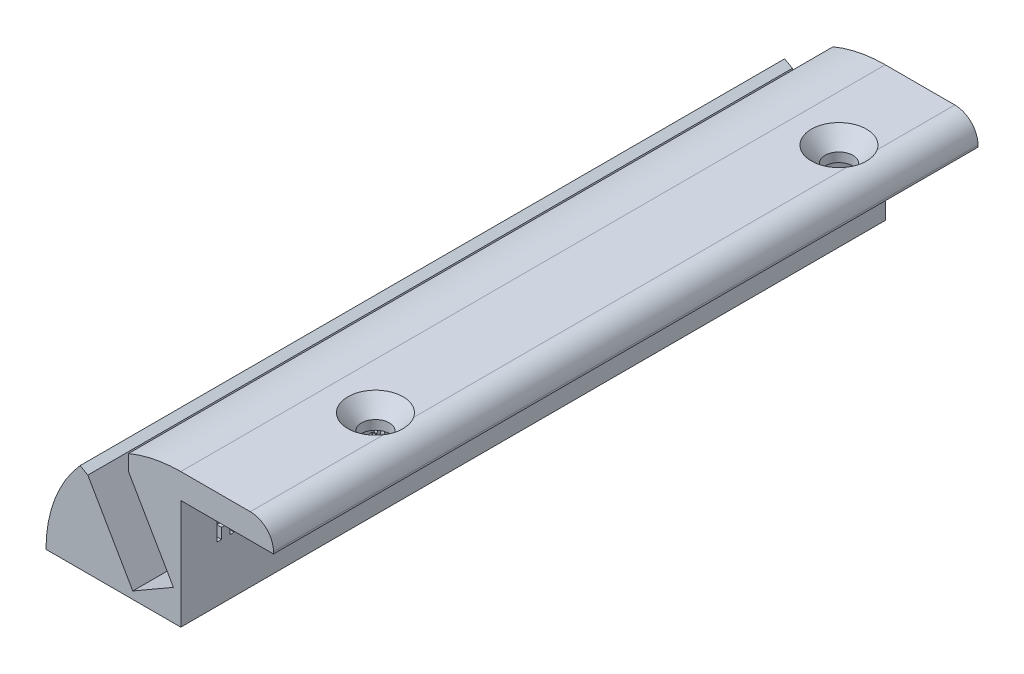
SolidWorks part; units mm, degrees
ref_plane "Front Plane" through (0, 0, 0) normal (0, 0, 1) x (1, 0, 0)
ref_plane "Top Plane" through (0, 0, 0) normal (0, 1, 0) x (1, 0, 0)
ref_plane "Right Plane" through (0, 0, 0) normal (1, 0, 0) x (0, 0, -1)
sketch "Sketch1" plane through (0, 0, 0) normal (0, 0, 1) x (1, 0, 0)
  line L0 (-43.8658, 7.3279) -> (-25.4, 7.3279)
  line L1 (-127, 7.3279) -> (127, 7.3279) construction
  line L2 (-25.4, 7.3279) -> (-25.4, 21.9837)
  line L3 (-25.4, 22.3647) -> (-14.6818, 22.3647)
  line L4 (-25.4, 21.9837) -> (228.6, 21.9837) construction
  line L5 (-25.4, 22.3647) -> (-25.4, 21.9837)
  line L6 (-38.1345, 19.0062) -> (-41.9445, 21.2059)
  line L7 (-41.9445, 21.2059) -> (-32.5693, 26.6187)
  line L8 (-32.5693, 26.6187) -> (-32.5693, 22.2193)
  line L9 (-25.4, 7.3279) -> (-34.6329, 23.3198) construction
  line L14 (-25.4, 25.7937) -> (-15.875, 25.7937)
  line L15 (-12.7, 22.6187) -> (-12.7, 22.3647)
  line L16 (-12.7, 22.3647) -> (-14.6818, 22.3647)
  line L18 (-38.1345, 19.0062) -> (-31.975, 8.3377)
  line L19 (-31.975, 8.3377) -> (-26.4098, 11.5508)
  line L20 (-26.4098, 11.5508) -> (-32.5693, 22.2193)
  line L21 (-32.5693, 22.2193) -> (-38.1345, 19.0062)
  line L22 (-38.1345, 19.0062) -> (-31.975, 8.3377)
  line L23 (-31.975, 8.3377) -> (-26.4098, 11.5508)
  line L24 (-26.4098, 11.5508) -> (-32.5693, 22.2193)
  line L25 (-32.5693, 22.2193) -> (-38.1345, 19.0062)
  circle A0 centre (-25.4, 7.3279) radius 18.4658
  arc A1 (-15.875, 25.7937) -> (-12.7, 22.6187) centre (-15.875, 22.6187) cw
  point P3 (-25.4, 25.7937)
  point P7 (-25.4, 21.9837)
  point P20 (-27.0497, 10.1852)
  dimension "D8" = 3.175
  dimension "D1" = 3.81
  dimension "D2" = 0.381
  dimension "D3" = 60
  dimension "D4" = 0.1905
  dimension "D5" = 30
  dimension "D6" = 30
  dimension "D7" = 3.81
  dimension "D9" = 12.7
extrude "Boss-Extrude1" add sketch "Sketch1" along normal mid plane 96.52 contours L0 L9 L23 L22 L6 A0 | L9 L2 L5 L3 A0 L8 L24 L23 | A1 L14 A0 L16 L15
ref_plane "Plane1" through (0, 0, -35.56) normal (0, 0, -1) x (-1, 0, 0)
sketch "Sketch4" plane through (0, 0, -35.56) normal (0, 0, -1) x (-1, 0, 0)
  line L0 (20.955, 22.3647) -> (20.955, 23.6347)
  line L1 (25.4, 22.3647) -> (12.7, 22.3647) construction
  line L2 (20.955, 23.6347) -> (24.267, 27.4447)
  line L3 (24.267, 27.4447) -> (19.05, 27.4447)
  line L4 (19.05, 27.4447) -> (19.05, 22.3647)
  line L5 (19.05, 22.3647) -> (20.955, 22.3647)
  point P7 (21.1325, 23.6347)
  dimension "D1" = 1.905
  dimension "D2" = 1.27
  dimension "D3" = 41
  dimension "D4" = 5.08
  dimension "D5" = 6.35
revolve "Cut-Revolve1" cut sketch "Sketch4" angle 360 about L4
pattern_linear "LPattern1" count 2 spacing 63.5 along (0, 0, 1) of "Cut-Revolve1"
sketch "Sketch5" plane through (-25.4, 0, 0) normal (1, 0, 0) x (0, 0, -1)
  line L0 (-69.1647, 14.9479) -> (67.826, 14.9479) construction
  line L1 (-48.26, 7.3279) -> (48.26, 7.3279) construction
  text T0 "<b>Headboard Ceiling LED Mount V1 3.8in</b>" font "Century Gothic" height 3.302
  point P3 (0, 14.9479)
  dimension "D1" = 7.62
extrude "Cut-Extrude2" cut sketch "Sketch5" against normal blind 0.635
